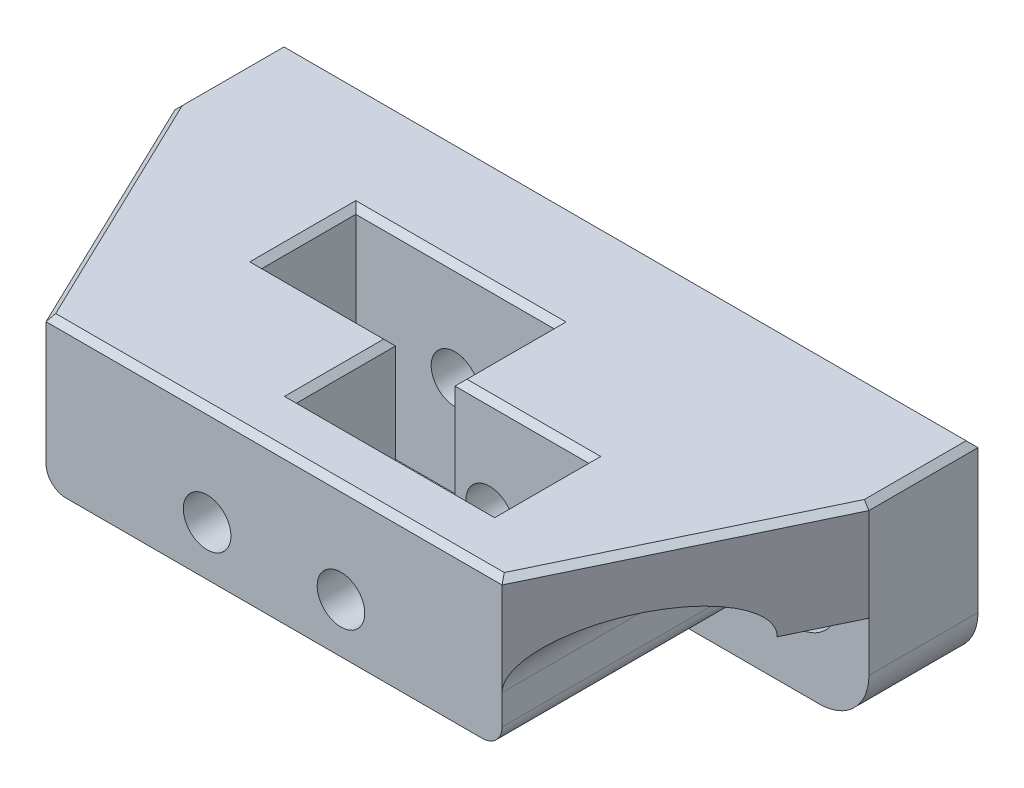
SolidWorks part; units mm, degrees
ref_plane "前视基准面" through (0, 0, 0) normal (0, 0, 1) x (1, 0, 0)
ref_plane "上视基准面" through (0, 0, 0) normal (0, 1, 0) x (1, 0, 0)
ref_plane "右视基准面" through (0, 0, 0) normal (1, 0, 0) x (0, 0, -1)
sketch "草图1" plane through (0, 0, 0) normal (0, 0, 1) x (1, 0, 0)
  line L1 (-13.125, 18.5417) -> (56.875, 18.5417)
  line L2 (-13.125, 18.5417) -> (-13.125, -1.4583)
  line L3 (-13.125, -1.4583) -> (56.875, -1.4583)
  line L4 (56.875, 18.5417) -> (56.875, -1.4583)
  dimension "D1" = 70
  dimension "D2" = 20
extrude "凸台-拉伸1" add sketch "草图1" along normal blind 11
sketch "草图3" plane through (0, 0, 11) normal (0, 0, 1) x (1, 0, 0)
  line L0 (56.875, -1.4583) -> (56.875, 18.5417) construction
  line L1 (-13.125, 18.5417) -> (56.875, 18.5417)
  line L2 (-13.125, 18.5417) -> (-13.125, 3.5417)
  line L3 (-13.125, 3.5417) -> (56.875, 3.5417)
  line L4 (56.875, 18.5417) -> (56.875, 3.5417)
  dimension "D1" = 15
extrude "凸台-拉伸2" add sketch "草图3" along normal blind 25
sketch "草图4" plane through (0, 3.5417, 0) normal (0, -1, 0) x (1, 0, 0)
  line L0 (-13.125, 36) -> (-13.125, 11)
  line L1 (-13.125, 36) -> (-13.125, 11) construction
  line L2 (-13.125, 11) -> (-1.125, 36)
  line L3 (-13.125, 36) -> (56.875, 36) construction
  line L4 (-1.125, 36) -> (-13.125, 36)
  line L5 (21.875, 36) -> (21.875, 10.9694) construction
  line L6 (-13.125, 11) -> (56.875, 11) construction
  line L7 (56.875, 11) -> (44.875, 36)
  line L8 (56.875, 36) -> (56.875, 11)
  line L9 (44.875, 36) -> (56.875, 36)
  line L10 (5.125, 11) -> (25.125, 11)
  line L15 (5.125, 11) -> (5.125, 20.5)
  line L17 (25.125, 11) -> (25.125, 21)
  line L18 (5.125, 20.5) -> (18.625, 20.5)
  line L19 (25.125, 21) -> (38.625, 21)
  line L20 (18.625, 21) -> (18.625, 30.5)
  line L21 (18.625, 30.5) -> (38.625, 30.5)
  line L22 (38.625, 21) -> (38.625, 30.5)
  line L23 (18.625, 21) -> (18.625, 20.5)
  dimension "D1" = 46
  dimension "D2" = 10
  dimension "D3" = 9.5
  dimension "D4" = 3.25
  dimension "D5" = 20
  dimension "D6" = 9.5
  dimension "D7" = 3.25
extrude "切除-拉伸1" cut sketch "草图4" against normal blind 15
sketch "草图5" plane through (0, 0, 36) normal (0, 0, 1) x (1, 0, 0)
  line L0 (21.875, 8.5417) -> (-13.125, 8.5417) construction
  line L3 (21.875, 18.5417) -> (21.875, -1.4583) construction
  line L4 (44.875, 18.5417) -> (-1.125, 18.5417) construction
  line L5 (-13.125, -1.4583) -> (56.875, -1.4583) construction
  line L7 (-13.125, 18.5417) -> (-13.125, 3.5417) construction
  circle A7 centre (-5.625, 8.5417) radius 4.5
  circle A8 centre (49.375, 8.5417) radius 4.5
  dimension "D1" = 9
  dimension "D2" = 27.5
extrude "切除-拉伸2" cut sketch "草图5" against normal blind 30
sketch "草图8" plane through (0, 0, 30.5) normal (0, 0, -1) x (-1, 0, 0)
  line L0 (-18.625, 18.5417) -> (-38.625, -1.4583) construction
  line L1 (-38.625, 3.5417) -> (-38.625, -1.4583) construction
  circle A0 centre (-28.625, 8.5417) radius 2.4
  dimension "D1" = 4.8
  dimension "D2" = 5
sketch "草图11" plane through (0, 0, 6) normal (0, 0, 1) x (1, 0, 0)
  circle A0 centre (-5.625, 8.5417) radius 2.6
  circle A1 centre (49.375, 8.5417) radius 2.6
  dimension "D1" = 5.2
  dimension "D2" = 5.2
extrude "切除-拉伸7" cut sketch "草图11" against normal blind 6
sketch "草图12" plane through (0, 0, 36) normal (0, 0, 1) x (1, 0, 0)
  line L0 (56.875, 18.5417) -> (56.875, 3.5417) construction
  line L1 (-13.125, 3.5417) -> (-1.125, 3.5417)
  line L2 (-13.125, 3.5417) -> (-13.125, 8.5417)
  line L3 (-13.125, 8.5417) -> (-1.125, 8.5417)
  line L4 (-1.125, 3.5417) -> (-1.125, 8.5417)
  line L5 (44.875, 3.5417) -> (56.875, 3.5417)
  line L6 (44.875, 3.5417) -> (44.875, 8.5417)
  line L7 (44.875, 8.5417) -> (56.875, 8.5417)
  line L8 (56.875, 3.5417) -> (56.875, 8.5417)
extrude "切除-拉伸8" cut sketch "草图12" against normal blind 25
extrude "切除-拉伸5" cut sketch "草图8" against normal through all both and the other way through all
sketch "草图10" plane through (0, 0, 11) normal (0, 0, 1) x (1, 0, 0)
  line L0 (5.125, -1.4583) -> (25.125, 18.5417) construction
  line L1 (-13.125, -1.4583) -> (56.875, -1.4583) construction
  line L2 (5.125, 3.5417) -> (5.125, -1.4583) construction
  circle A0 centre (15.125, 8.5417) radius 2.4
  dimension "D1" = 4.8
extrude "切除-拉伸6" cut sketch "草图10" against normal through all both and the other way through all
fillet "圆角1" radius 5 2 edges at (-13.125, -1.4583, 5.5) (56.875, -1.4583, 5.5)
chamfer "倒角1" distance 0.6 angle 45 14 edges at (21.875, 18.5417, 0) (56.875, 18.5417, 5.5) (50.875, 18.5417, 23.5) (21.875, 18.5417, 36) (-7.125, 18.5417, 23.5) (-13.125, 18.5417, 5.5) (18.625, 18.5417, 25.5) (28.625, 18.5417, 30.5) (38.625, 18.5417, 25.75) (31.875, 18.5417, 21) (25.125, 18.5417, 16) (15.125, 18.5417, 11) (5.125, 18.5417, 15.75) (11.875, 18.5417, 20.5)
fillet "圆角2" radius 2 4 edges at (25.125, 3.5417, 16) (18.625, 3.5417, 25.5) (44.875, 3.5417, 23.5) (-1.125, 3.5417, 23.5)
